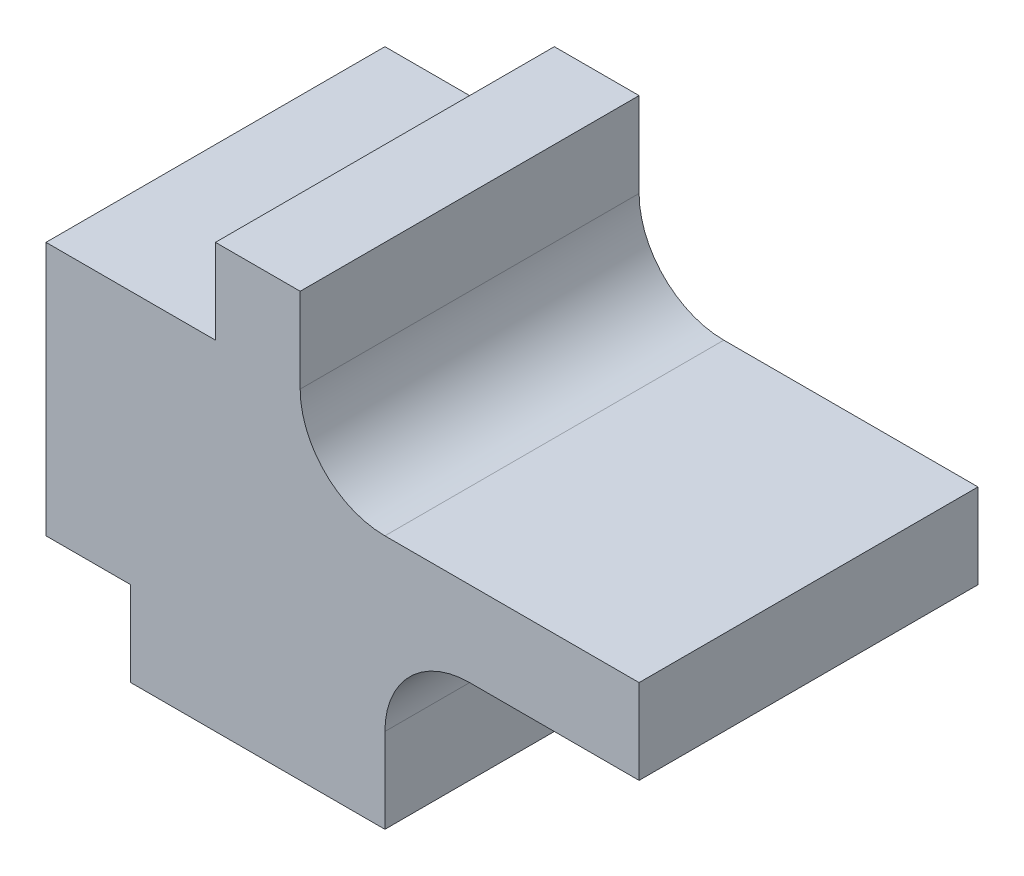
SolidWorks part; units mm, degrees
ref_plane "前基準面" through (0, 0, 0) normal (0, 0, 1) x (1, 0, 0)
ref_plane "上基準面" through (0, 0, 0) normal (0, 1, 0) x (1, 0, 0)
ref_plane "右基準面" through (0, 0, 0) normal (1, 0, 0) x (0, 0, -1)
sketch "草圖1" plane through (0, 0, 0) normal (0, 0, 1) x (1, 0, 0)
  line L0 (0, 0) -> (3, 0)
  line L1 (3, 0) -> (3, 1)
  line L2 (4, 2) -> (6, 2)
  line L3 (6, 2) -> (6, 3)
  line L4 (6, 3) -> (3, 3)
  line L5 (2, 4) -> (2, 5)
  line L6 (2, 5) -> (1, 5)
  line L7 (1, 5) -> (1, 4)
  line L8 (1, 4) -> (-1, 4)
  line L9 (-1, 4) -> (-1, 1)
  line L10 (-1, 1) -> (0, 1)
  line L11 (0, 1) -> (0, 0)
  arc A0 (3, 3) -> (2, 4) centre (3, 4) cw
  arc A1 (3, 1) -> (4, 2) centre (4, 1) cw
  point P10 (4.5, 3)
  point P17 (2, 3)
  point P20 (3, 2)
  dimension "D11" = 1
  dimension "D1" = 1
  dimension "D2" = 3
  dimension "D3" = 2
  dimension "D4" = 7
  dimension "D5" = 1
  dimension "D6" = 1
  dimension "D7" = 4
  dimension "D8" = 5
  dimension "D9" = 3
  dimension "D10" = 1
extrude "填料-伸長1" add sketch "草圖1" along normal blind 4
